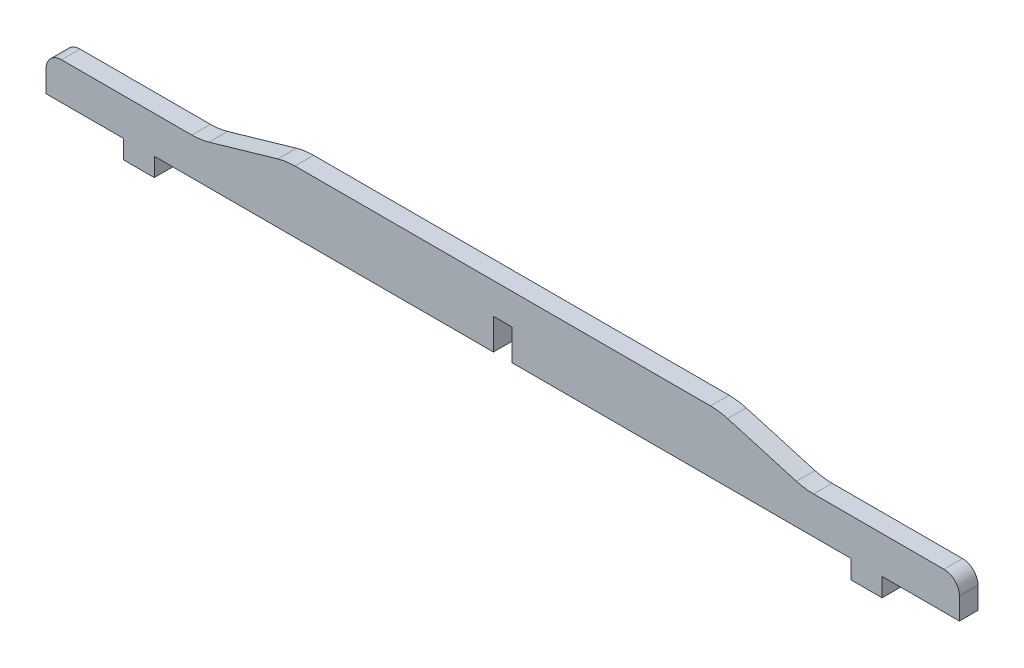
SolidWorks part; units mm, degrees
ref_plane "Front Plane" through (0, 0, 0) normal (0, 0, 1) x (1, 0, 0)
ref_plane "Top Plane" through (0, 0, 0) normal (0, 1, 0) x (1, 0, 0)
ref_plane "Right Plane" through (0, 0, 0) normal (1, 0, 0) x (0, 0, -1)
sketch "Sketch1" plane through (0, 0, 0) normal (0, 0, 1) x (1, 0, 0)
  line L0 (70, 0) -> (-70, 0)
  line L4 (112.6667, -20) -> (-112.6667, -20)
  line L5 (-147.6667, -20) -> (-122.6667, -20)
  line L6 (147.6667, -20) -> (122.6667, -20)
  line L7 (-122.6667, -20) -> (-122.6667, -26)
  line L8 (-122.6667, -26) -> (-112.6667, -26)
  line L9 (-112.6667, -26) -> (-112.6667, -20)
  line L10 (112.6667, -20) -> (112.6667, -26)
  line L11 (112.6667, -26) -> (122.6667, -26)
  line L12 (122.6667, -26) -> (122.6667, -20)
  line L13 (-147.6667, -20) -> (-147.6667, -8)
  line L14 (-147.6667, -8) -> (-97.6667, -8)
  line L15 (-97.6667, -8) -> (-70, 0)
  line L16 (70, 0) -> (97.6667, -8)
  line L17 (97.6667, -8) -> (147.6667, -8)
  line L18 (147.6667, -8) -> (147.6667, -20)
  point P4 (0, 0)
  point P10 (0, -20)
  dimension "D1" = 295.3333
  dimension "D2" = 20
  dimension "D3" = 6
  dimension "D4" = 10
  dimension "D7" = 12
  dimension "D5" = 50
  dimension "D6" = 140
  dimension "D8" = 25
extrude "Boss-Extrude1" add sketch "Sketch1" along normal blind 6
fillet "Fillet1" radius 5 2 edges at (147.6667, -8, 3) (-147.6667, -8, 3)
fillet "Fillet2" radius 20 4 edges at (97.6667, -8, 3) (70, 0, 3) (-70, 0, 3) (-97.6667, -8, 3)
sketch "Sketch2" plane through (0, 0, 6) normal (0, 0, 1) x (1, 0, 0)
  line L0 (0, 0) -> (0, -20) construction
  line L1 (67.1665, 0) -> (-67.1665, 0) construction
  line L2 (-112.6667, -20) -> (112.6667, -20) construction
  line L4 (-3, -20) -> (3, -20)
  line L5 (-3, -20) -> (-3, -10)
  line L6 (-3, -10) -> (3, -10)
  line L7 (3, -20) -> (3, -10)
  point P10 (0, -10)
  dimension "D1" = 6
extrude "Cut-Extrude1" cut sketch "Sketch2" against normal through all both and the other way through all
equation "\"D1@Sketch1\"=300-4.66666666"
